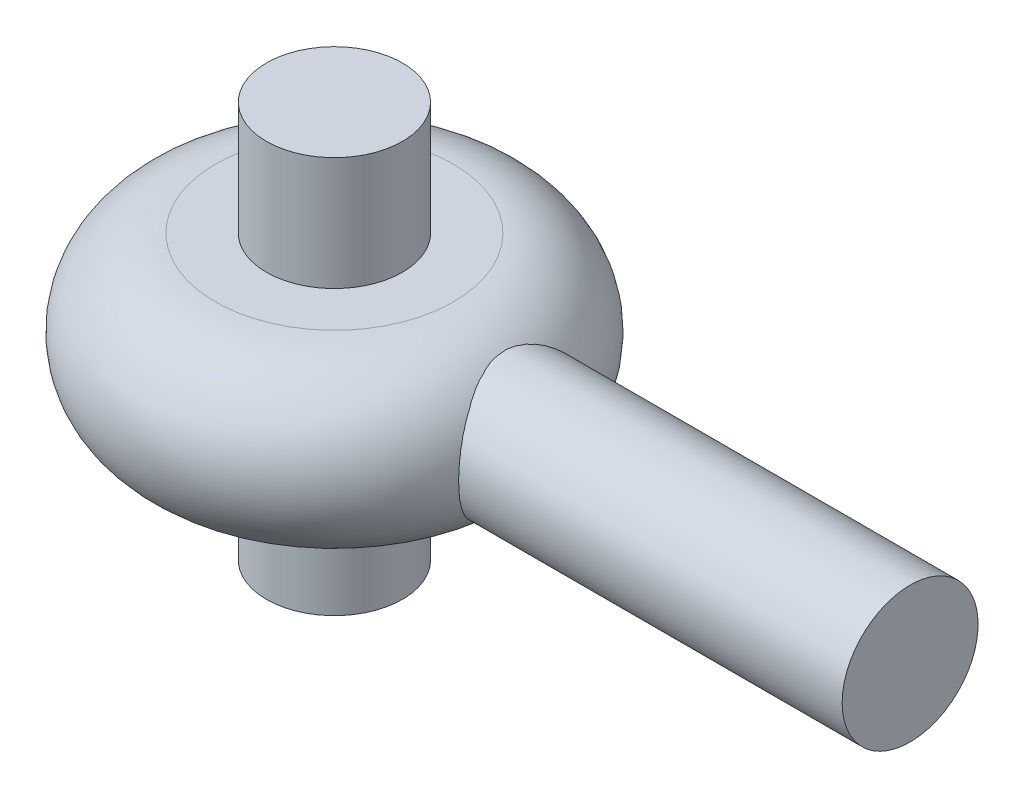
SolidWorks part; units mm, degrees
ref_plane "Front Plane" through (0, 0, 0) normal (0, 0, 1) x (1, 0, 0)
ref_plane "Top Plane" through (0, 0, 0) normal (0, 1, 0) x (1, 0, 0)
ref_plane "Right Plane" through (0, 0, 0) normal (1, 0, 0) x (0, 0, -1)
sketch "Sketch1" plane through (0, 0, 0) normal (0, 1, 0) x (1, 0, 0)
  line L0 (0, 0) -> (50.8, 0) construction
  line L1 (50.8, 0) -> (10.0163, 0)
  circle A1 centre (0, 0) radius 12.7
  dimension "D1" = 40.7837
  dimension "D2" = 25.4
  dimension "D3" = 50.8
sketch "Sketch3" plane through (0, 0, 0) normal (1, 0, 0) x (0, 0, -1)
  line L0 (0, 0) -> (0, 8.1279) construction
  line L2 (6, 7.5) -> (10.5165, 7.5)
  line L3 (6, 7.5) -> (6, -7.5)
  line L5 (0, 0) -> (6, 0) construction
  line L6 (6, -7.5) -> (10.5165, -7.5)
  arc A2 (10.5165, 7.5) -> (10.5165, -7.5) centre (10.5165, 0) cw
  dimension "D1" = 6
  dimension "D2" = 15
revolve "Revolve2" add sketch "Sketch3" angle 360 about L0
other "Solidprofiles 12MM(1)"
ref_plane "Plane2" through (50.8, 0, 0) normal (-1, 0, 0) x (0, 0, 1)
sketch "Sketch14" plane through (50.8, 0, 0) normal (-1, 0, 0) x (0, 0, 1)
  circle A0 centre (0, 0) radius 6
  point P3 (0, 0)
  dimension "D1" = 12
sketch "Sketch15" plane through (0, 7.5, 0) normal (0, 1, 0) x (1, 0, 0)
  circle A0 centre (0, 0) radius 6
extrude "Boss-Extrude1" add sketch "Sketch15" along normal blind 10 and the other way blind 25 separate body
